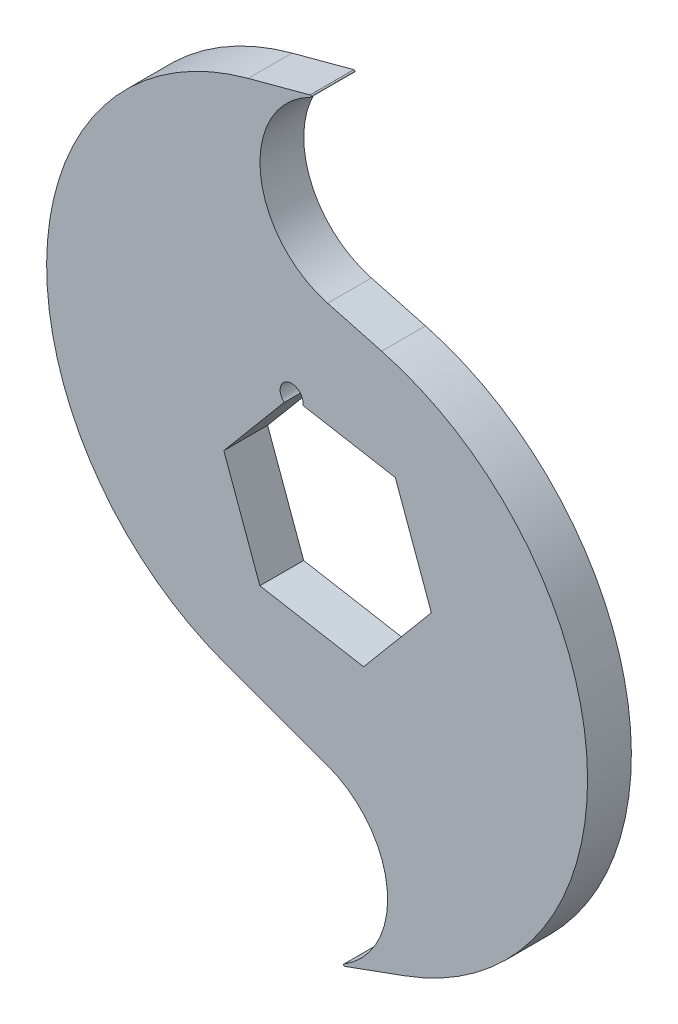
SolidWorks part; units mm, degrees
ref_plane "Front Plane" through (0, 0, 0) normal (0, 0, 1) x (1, 0, 0)
ref_plane "Top Plane" through (0, 0, 0) normal (0, 1, 0) x (1, 0, 0)
ref_plane "Right Plane" through (0, 0, 0) normal (1, 0, 0) x (0, 0, -1)
sketch "Sketch1" plane through (0, 0, 0) normal (0, 0, 1) x (1, 0, 0)
  line L0 (0, 52.07) -> (-11.0405, 49.1117)
  line L1 (0, 52.07) -> (0, 0) construction
  line L2 (0, -52.07) -> (10.7407, -48.1607)
  line L3 (0, 0) -> (0, -52.07) construction
  line L5 (-5.0156, 13.7803) -> (-14.4419, 2.5465)
  line L6 (-14.4419, 2.5465) -> (-9.4263, -11.2338)
  line L7 (-9.4263, -11.2338) -> (5.0156, -13.7803)
  line L8 (5.0156, -13.7803) -> (14.4419, -2.5465)
  line L9 (14.4419, -2.5465) -> (9.4263, 11.2338)
  line L10 (9.4263, 11.2338) -> (-5.0156, 13.7803)
  line L11 (0, 27.5355) -> (7.5237, 25.5195)
  line L12 (0, -28.2018) -> (-14.1906, -23.0368)
  circle A0 centre (0, 0) radius 52.07 construction
  arc A1 (0, 52.07) -> (0, 27.5355) centre (3.287, 39.8027) ccw
  arc A3 (0, -52.07) -> (0, -28.2018) centre (-4.3437, -40.1359) ccw
  arc A4 (10.7407, -48.1607) -> (7.5237, 25.5195) centre (-2.4834, -11.8278) ccw
  arc A5 (-11.0405, 49.1117) -> (-14.1906, -23.0368) centre (-1.2414, 12.5408) ccw
  circle A6 centre (0, 0) radius 12.7 construction
  circle A7 centre (-5.0156, 13.7803) radius 1.5875
  dimension "D4" = 70
  dimension "D5" = 25.4
  dimension "D1" = 104.14
  dimension "D6" = 12.7
  dimension "D8" = 3.175
  dimension "D2" = 11.43
  dimension "D3" = 75
  dimension "D7" = 20
extrude "Boss-Extrude1" add sketch "Sketch1" along normal mid plane 6.096 contours L0 A5 L12 A3 L2 A4 L11 A1 A7 L10 L9 L8 L7 L6 L5
fillet "Fillet1" radius 0.127 2 edges at (0, 52.07, 0) (0, -52.07, 0)
